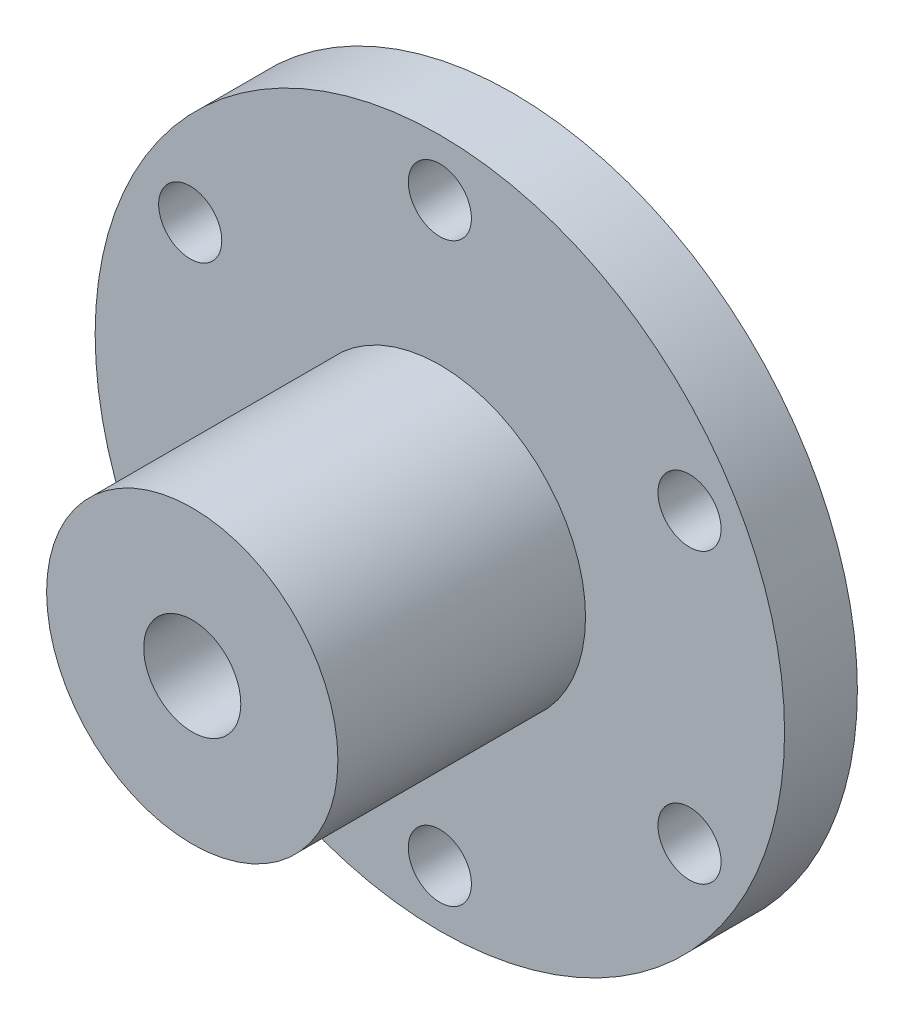
SolidWorks part; units mm, degrees
ref_plane "Front Plane" through (0, 0, 0) normal (0, 0, 1) x (1, 0, 0)
ref_plane "Top Plane" through (0, 0, 0) normal (0, 1, 0) x (1, 0, 0)
ref_plane "Right Plane" through (0, 0, 0) normal (1, 0, 0) x (0, 0, -1)
sketch "Sketch1" plane through (0, 0, 0) normal (0, 0, 1) x (1, 0, 0)
  circle A0 centre (0, 0) radius 28.4
  circle A1 centre (0, 23.75) radius 2.6
  circle A2 centre (20.5681, 11.875) radius 2.6
  circle A3 centre (20.5681, -11.875) radius 2.6
  circle A4 centre (0, -23.75) radius 2.6
  circle A5 centre (-20.5681, -11.875) radius 2.6
  circle A6 centre (-20.5681, 11.875) radius 2.6
  circle A7 centre (0, 0) radius 4
  dimension "D1" = 56.8
  dimension "D2" = 5.2
  dimension "D3" = 23.75
  dimension "D5" = 8
  dimension "D4" = 6
extrude "Boss-Extrude1" add sketch "Sketch1" along normal blind 6
sketch "Sketch2" plane through (0, 0, 6) normal (0, 0, 1) x (1, 0, 0)
  circle A0 centre (0, 0) radius 12
  circle A1 centre (0, 0) radius 4
  dimension "D1" = 8
  dimension "D2" = 24
extrude "Boss-Extrude2" add sketch "Sketch2" along normal blind 20.4
